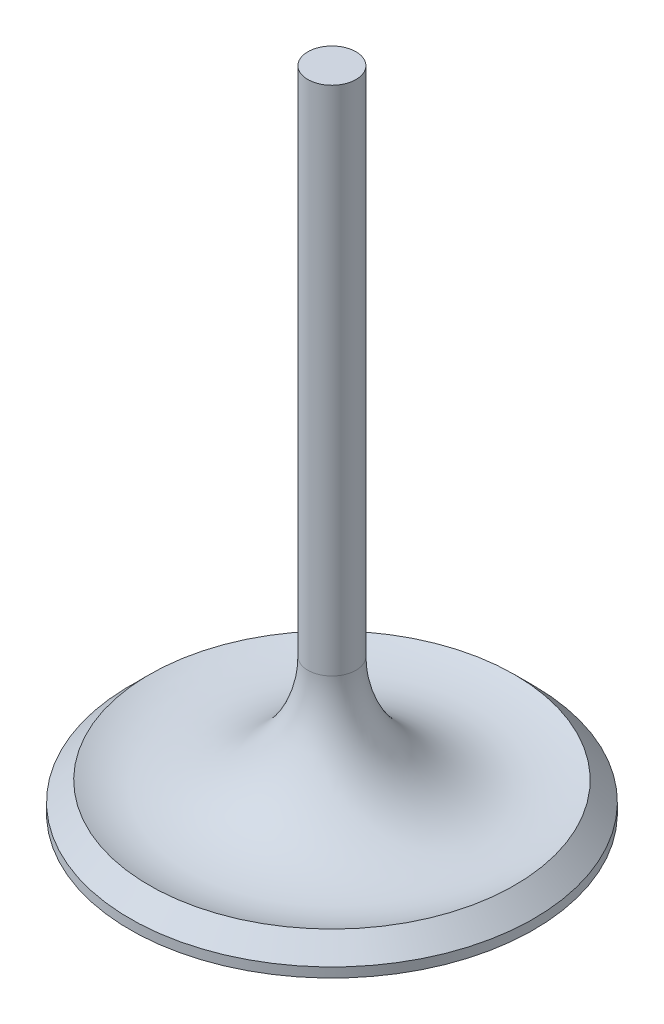
SolidWorks part; units mm, degrees
ref_plane "Front Plane" through (0, 0, 0) normal (0, 0, 1) x (1, 0, 0)
ref_plane "Top Plane" through (0, 0, 0) normal (0, 1, 0) x (1, 0, 0)
ref_plane "Right Plane" through (0, 0, 0) normal (1, 0, 0) x (0, 0, -1)
sketch "Sketch1" plane through (0, 0, 0) normal (0, 0, 1) x (1, 0, 0)
  line L0 (0, 0) -> (0, 85.55)
  line L1 (0, 85.55) -> (3.18, 85.55)
  line L2 (3.18, 85.55) -> (3.18, 17.9547)
  line L3 (24.13, 3.81) -> (26.67, 1.27)
  line L4 (26.67, 1.27) -> (26.67, 0)
  line L5 (26.67, 0) -> (0, 0)
  arc A0 (3.18, 17.9547) -> (24.13, 3.81) centre (18.43, 17.9547) ccw
  dimension "D7" = 15.25
  dimension "D1" = 26.67
  dimension "D2" = 85.55
  dimension "D3" = 3.18
  dimension "D4" = 1.27
  dimension "D5" = 3.81
  dimension "D6" = 45
revolve "Revolve1" add sketch "Sketch1" angle 360 about L0
